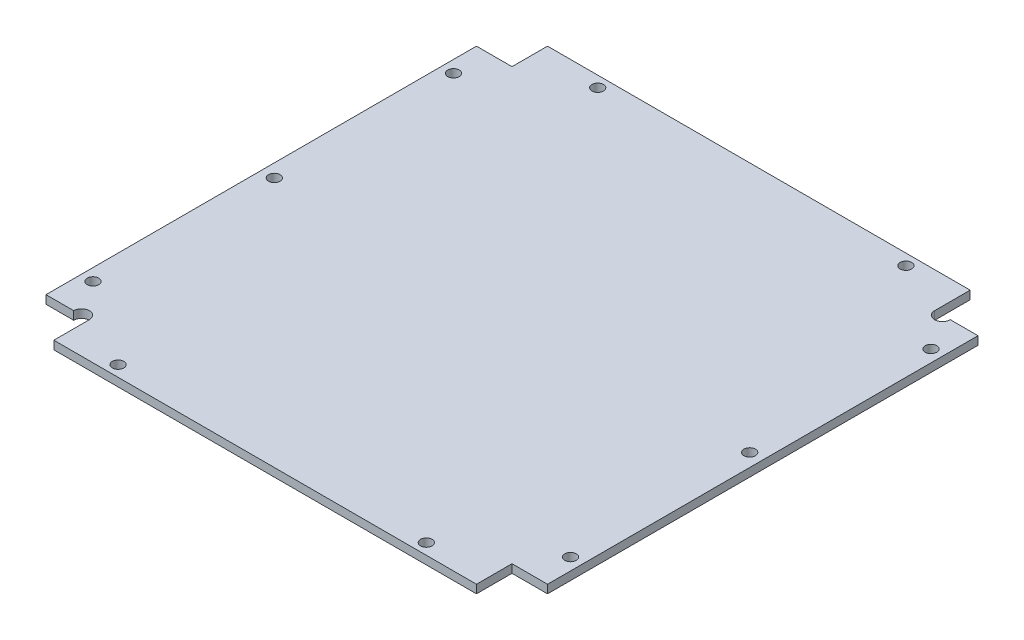
SolidWorks part; units mm, degrees
material "電力回路基板"
ref_plane "Front Plane" through (0, 0, 0) normal (0, 0, 1) x (1, 0, 0)
ref_plane "Top Plane" through (0, 0, 0) normal (0, 1, 0) x (1, 0, 0)
ref_plane "Right Plane" through (0, 0, 0) normal (1, 0, 0) x (0, 0, -1)
sketch "Sketch1" plane through (0, 0, 0) normal (0, 1, 0) x (1, 0, 0)
  line L0 (-35.6444, 8.9071) -> (-28.8444, 8.9071)
  line L1 (-28.8444, 15.7071) -> (52.0556, 15.7071)
  line L2 (52.0556, 15.7071) -> (52.0556, 8.9071)
  line L3 (52.0556, 8.9071) -> (60.3556, 8.9071)
  line L4 (60.3556, 8.9071) -> (60.3556, -73.4929)
  line L5 (60.3556, -73.4929) -> (53.5556, -73.4929)
  line L6 (53.5556, -73.4929) -> (53.5556, -80.2929)
  line L7 (53.5556, -80.2929) -> (-27.3444, -80.2929)
  line L8 (-27.3444, -80.2929) -> (-27.3444, -73.4929)
  line L9 (-27.3444, -73.4929) -> (-35.6444, -73.4929)
  line L10 (-35.6444, -73.4929) -> (-35.6444, 8.9071)
  line L11 (-28.8444, 8.9071) -> (-28.8444, 15.7071)
  dimension "D1" = 6.8
  dimension "D2" = 6.8
  dimension "D3" = 6.8
  dimension "D4" = 6.8
  dimension "D5" = 96
  dimension "D6" = 6.8
  dimension "D7" = 8.3
  dimension "D8" = 6.8
  dimension "D9" = 96
  dimension "D10" = 8.3
extrude "Boss-Extrude1" add sketch "Sketch1" along normal blind 1.6 contours L10 L0 L11 L1 L2 L3 L4 L5 L6 L7 L8 L9
hole_wizard "Ø2.2 (2.2) 直径の穴1" positions "Sketch11" profile "Sketch10" hole size "Ø2.2" standard "Ansi Metric"
sketch "Sketch11" plane through (0, 1.6, 0) normal (0, 1, 0) x (1, 0, 0)
  line L3 (-28.8444, 15.7071) -> (52.0556, 15.7071) construction
  line L5 (-27.3444, -73.4929) -> (-35.6444, -73.4929) construction
  line L6 (53.5556, -73.4929) -> (53.5556, -80.2929) construction
  line L8 (53.5556, -80.2929) -> (-27.3444, -80.2929) construction
  line L10 (52.0556, 8.9071) -> (60.3556, 8.9071) construction
  line L11 (52.0556, 15.7071) -> (52.0556, 8.9071) construction
  line L12 (60.3556, 8.9071) -> (60.3556, -73.4929) construction
  line L13 (-35.6444, -73.4929) -> (-35.6444, 8.9071) construction
  line L14 (-28.8444, 15.7071) -> (52.0556, 15.7071) construction
  line L15 (-28.8444, 8.9071) -> (-28.8444, 15.7071) construction
  line L16 (-27.3444, -80.2929) -> (-27.3444, -73.4929) construction
  point P0 (57.8556, -32.2929)
  point P2 (-33.1444, -32.2929)
  point P4 (41.8556, -78.1929)
  point P6 (41.8556, 13.6071)
  point P54 (-17.1444, 13.6071)
  point P61 (-17.1444, -78.1929)
  dimension "D2" = 2.1
  dimension "D3" = 2.5
  dimension "D4" = 2.1
  dimension "D5" = 41.2
  dimension "D6" = 41.2
  dimension "D7" = 11.7
  dimension "D8" = 2.5
  dimension "D9" = 2.1
  dimension "D10" = 11.7
  dimension "D11" = 10.2
  dimension "D12" = 2.1
  dimension "D19" = 10.2
sketch "Sketch10" plane through (57.8556, 1.6, 32.2929) normal (1, 0, 0) x (0, 0, 1)
  line L0 (0, 0) -> (0, 2)
  line L1 (0, 2) -> (1.1, 2)
  line L2 (1.1, 2) -> (1.1, 0)
  line L5 (1.1, 0) -> (0, 0)
  line L10 (0, 2) -> (-1.1, 2) construction
  line L11 (0, -6.35) -> (0, 107.95) construction
  dimension "Hole Dia." = 2.2
  dimension "Hole Depth" = 2
  dimension "Drill Angle" = 180
sketch "Sketch12" plane through (0, 1.6, 0) normal (0, 1, 0) x (1, 0, 0)
  line L0 (52.0556, 8.9071) -> (60.3556, 8.9071) construction
  line L1 (-27.3444, -73.4929) -> (-35.6444, -73.4929) construction
  line L2 (60.3556, 8.9071) -> (60.3556, -73.4929) construction
  line L3 (-35.6444, -73.4929) -> (-35.6444, 8.9071) construction
  circle A0 centre (53.5556, 8.9071) radius 1.5
  circle A1 centre (-28.8444, -73.4929) radius 1.5
  dimension "D1" = 3
  dimension "D2" = 3
  dimension "D3" = 6.8
  dimension "D4" = 6.8
extrude "Cut-Extrude1" cut sketch "Sketch12" against normal through all
sketch "Sketch13" plane through (0, 1.6, 0) normal (0, 1, 0) x (1, 0, 0)
  line L0 (55.0556, 8.9071) -> (60.3556, 8.9071) construction
  line L1 (60.3556, -73.4929) -> (53.5556, -73.4929) construction
  line L2 (-30.3444, -73.4929) -> (-35.6444, -73.4929) construction
  line L3 (-35.6444, 8.9071) -> (-28.8444, 8.9071) construction
  line L4 (60.3556, 8.9071) -> (60.3556, -73.4929) construction
  line L5 (-35.6444, -73.4929) -> (-35.6444, 8.9071) construction
  point P0 (58.0556, 2.2071)
  point P1 (58.0556, -66.7929)
  point P2 (-33.3444, 2.2071)
  point P3 (-33.3444, -66.7929)
  dimension "D1" = 6.7
  dimension "D2" = 6.7
  dimension "D3" = 6.7
  dimension "D4" = 6.7
  dimension "D5" = 2.3
  dimension "D6" = 2.3
  dimension "D7" = 2.3
  dimension "D8" = 2.3
hole_wizard "Ø2.2 (2.2) 直径の穴2" positions "Sketch15" profile "Sketch14" hole size "Ø2.2" standard "Ansi Metric"
sketch "Sketch15" plane through (0, 1.6, 0) normal (0, 1, 0) x (1, 0, 0)
  point P0 (-33.3444, 2.2071)
  point P3 (-33.3444, -66.7929)
  point P6 (58.0556, -66.7929)
  point P9 (58.0556, 2.2071)
sketch "Sketch14" plane through (-33.3444, 1.6, -2.2071) normal (1, 0, 0) x (0, 0, 1)
  line L0 (0, 0) -> (0, 1.6)
  line L1 (0, 1.6) -> (1.1, 1.6)
  line L2 (1.1, 1.6) -> (1.1, 0)
  line L5 (1.1, 0) -> (0, 0)
  line L10 (0, 1.6) -> (-1.1, 1.6) construction
  line L11 (0, -6.35) -> (0, 107.95) construction
  dimension "穴の直径" = 2.2
  dimension "穴の深さ" = 1.6
  dimension "ﾄﾞﾘﾙ角度" = 180
